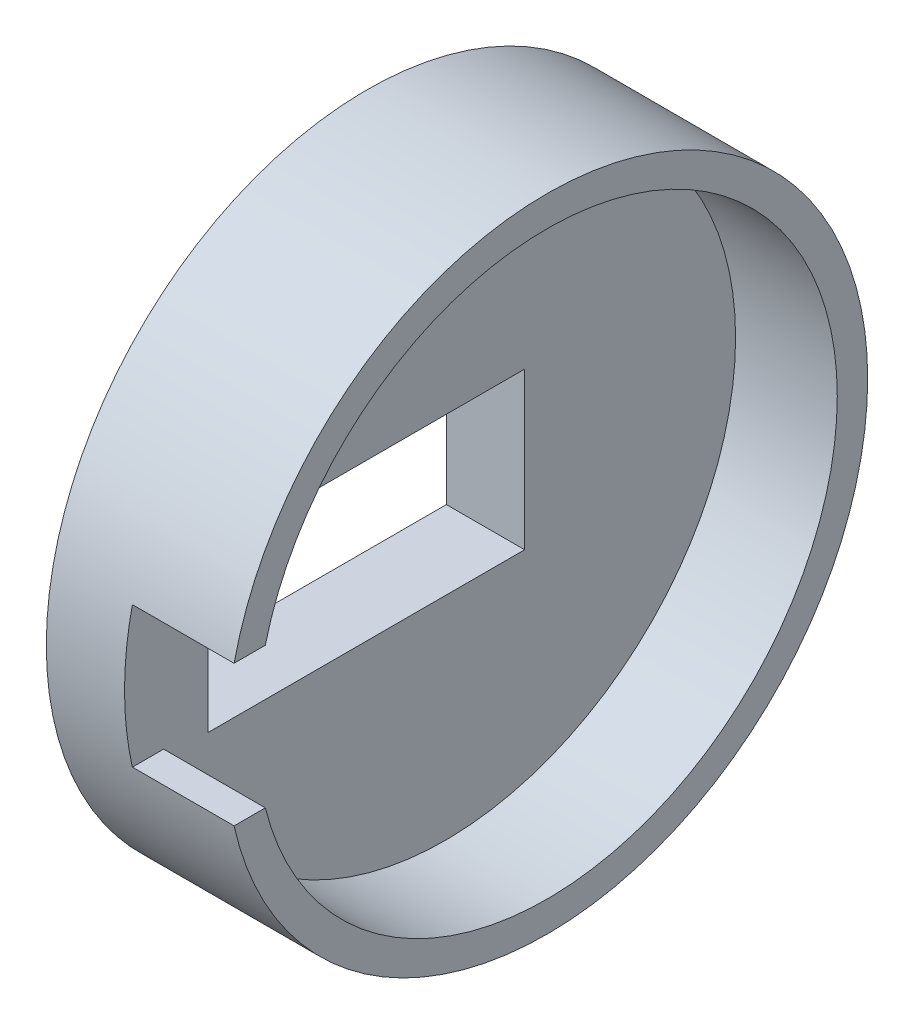
SolidWorks part; units mm, degrees
ref_plane "Alzado" through (0, 0, 0) normal (0, 0, 1) x (1, 0, 0)
ref_plane "Planta" through (0, 0, 0) normal (0, 1, 0) x (1, 0, 0)
ref_plane "Vista lateral" through (0, 0, 0) normal (1, 0, 0) x (0, 0, -1)
sketch "Croquis1" plane through (0, 0, 0) normal (1, 0, 0) x (0, 0, -1)
  circle A8 centre (0, 26) radius 11.1125
  circle A9 centre (0, 26) radius 3.175
  circle A10 centre (0, 26) radius 2.5
  circle A11 centre (0, 26) radius 15
  circle A12 centre (0, 0) radius 37.1125
  circle A13 centre (0, 0) radius 41
extrude "Saliente-Extruir1" add sketch "Croquis1" along normal blind 10 contours A11 A13 A12 | A12 A11
sketch "Croquis2" plane through (0, 0, 0) normal (-1, 0, 0) x (0, 0, 1)
  circle A0 centre (0, 0) radius 41
extrude "Saliente-Extruir2" add sketch "Croquis2" along normal blind 10
sketch "Croquis3" plane through (0, 0, 0) normal (1, 0, 0) x (0, 0, -1)
  line L1 (0, 0) -> (0, 14.8875)
  circle A10 centre (0, 0) radius 29.25
  circle A11 centre (0, 0) radius 23.25
  dimension "D1" = 46.5
  dimension "D2" = 58.5
extrude "Cortar-Extruir3" cut sketch "Croquis3" against normal blind 5 contours A10 A11
sketch "Croquis6" plane through (-10, 0, 0) normal (-1, 0, 0) x (0, 0, 1)
  circle A0 centre (0, 0) radius 41
extrude "Saliente-Extruir4" add sketch "Croquis6" along normal blind 5
sketch "Croquis8" plane through (10, 0, 0) normal (1, 0, 0) x (0, 0, -1)
  circle A0 centre (0, 0) radius 41
  circle A1 centre (0, 0) radius 34.6125
  dimension "D1" = 69.225
extrude "Saliente-Extruir9" add sketch "Croquis8" against normal blind 2
sketch "Croquis9" plane through (0, 0, 0) normal (1, 0, 0) x (0, 0, -1)
  circle A0 centre (0, 0) radius 6
  dimension "D1" = 12
sketch "Croquis10" plane through (-15, 0, 0) normal (-1, 0, 0) x (0, 0, 1)
  line L0 (30.3589, -10) -> (30.3589, 10)
  line L1 (30.3589, 10) -> (-10.1411, 10)
  line L2 (-10.1411, 10) -> (-10.1411, -10)
  line L3 (-10.1411, -10) -> (30.3589, -10)
extrude "Cortar-Extruir5" cut sketch "Croquis10" against normal blind 25
sketch "Croquis11" plane through (10, 0, 0) normal (1, 0, 0) x (0, 0, -1)
  circle A1 centre (0, 0) radius 41
  circle A2 centre (0, 0) radius 34.6125
extrude "Cortar-Extruir7" cut sketch "Croquis11" against normal blind 2
sketch "Croquis16" plane through (0, 0, 0) normal (1, 0, 0) x (0, 0, -1)
  circle A0 centre (0, 0) radius 37.1125
  circle A1 centre (0, 0) radius 23.25
  circle A2 centre (-25.2488, -14.5041) radius 0.1317
  circle A3 centre (0, 0) radius 29.25
extrude "Cortar-Extruir8" cut sketch "Croquis16" against normal blind 5 contours A1
sketch "Croquis17" plane through (8, 0, 0) normal (1, 0, 0) x (0, 0, -1)
  line L0 (-30.3589, -9) -> (-40, -9)
  line L1 (-30.3589, -10) -> (-30.3589, 10) construction
  line L2 (-37.3589, -9) -> (-30.3589, -9) construction
  line L3 (-30.3589, 9) -> (-40, 9)
  line L4 (-37.3589, 9) -> (-30.3589, 9) construction
  line L5 (-30.3589, 9) -> (-30.3589, -9)
  line L6 (-40, 9) -> (-52.1205, 3.6961)
  line L7 (-52.1205, 3.6961) -> (-39.9903, -9)
  circle A0 centre (0, 0) radius 41 construction
  circle A1 centre (-29.4297, -28.8275) radius 0.1962
  circle M1 centre (0, 0) radius 37.1125
  circle M2 centre (0, 0) radius 41
extrude "Cortar-Extruir11" cut sketch "Croquis17" against normal blind 13 contours L6 L7 M2 | L5 L3 L0 M1 | L7 L0 L3 M2 M1
sketch "Croquis18" plane through (-5, 0, 0) normal (1, 0, 0) x (0, 0, -1)
  line L1 (0, 0) -> (13.9516, 0)
  line L2 (0, -37.1125) -> (0, -41.5562)
  line L3 (0, 26) -> (0, 21.5562)
  arc A0 (0, -37.1125) -> (0, 37.1125) centre (0, 0) ccw
  arc A1 (0, -26) -> (0, 26) centre (0, 0) ccw
  arc A2 (0, 37.1125) -> (0, 26) centre (0, 31.5562) ccw
  arc A3 (0, -37.1125) -> (0, -26) centre (0, -31.5562) cw
  arc A4 (0, -21.5562) -> (0, -41.5562) centre (0, -31.5562) ccw
  arc A5 (0, -21.5562) -> (0, 21.5562) centre (0, 0) ccw
  arc A6 (0, 21.5562) -> (0, 41.5562) centre (0, 31.5562) cw
  arc A7 (0, -41.5562) -> (0, 41.5562) centre (0, 0) ccw
  arc A8 (-8.9499, -36.0172) -> (0, 37.1125) centre (0, 0) ccw
  dimension "D1" = 74.225
  dimension "D2" = 52
  dimension "D3" = 20
sketch "Croquis19" plane through (8, 0, 0) normal (1, 0, 0) x (0, 0, -1)
  circle A0 centre (0, 0) radius 41
  circle A1 centre (0, 0) radius 37.1125
